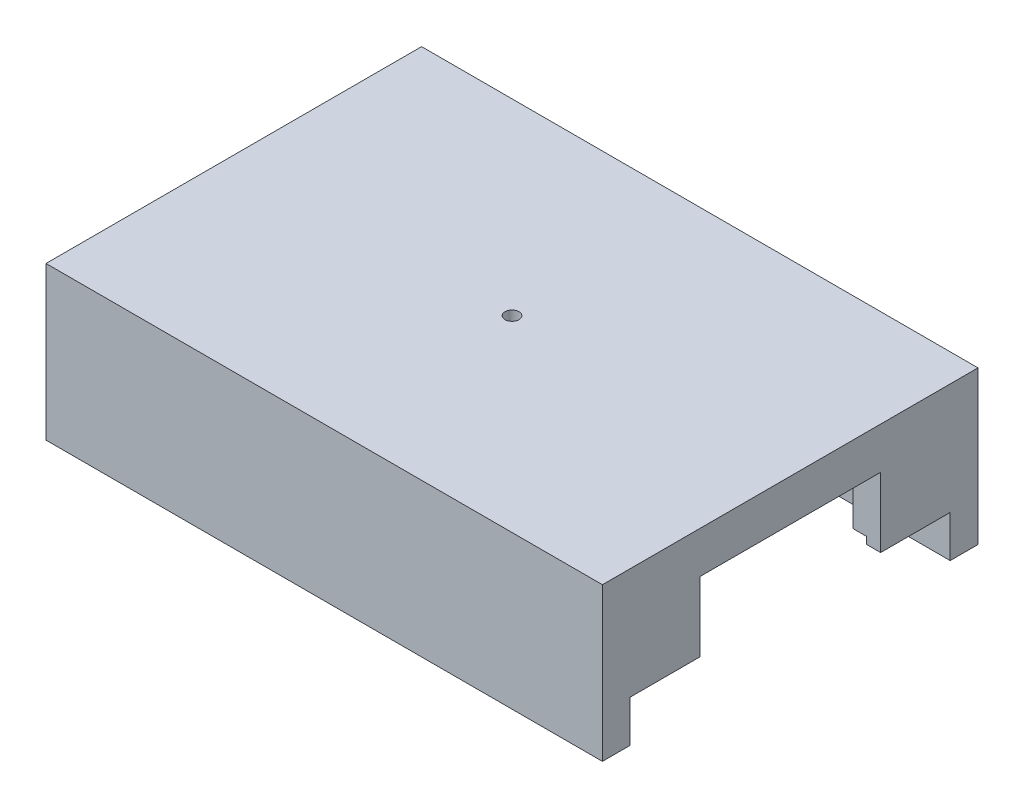
SolidWorks part; units mm, degrees
ref_plane "Front Plane" through (0, 0, 0) normal (0, 0, 1) x (1, 0, 0)
ref_plane "Top Plane" through (0, 0, 0) normal (0, 1, 0) x (1, 0, 0)
ref_plane "Right Plane" through (0, 0, 0) normal (1, 0, 0) x (0, 0, -1)
sketch "Sketch1" plane through (0, 0, 0) normal (0, 1, 0) x (1, 0, 0)
  line L1 (-11.5, 11.5) -> (11.5, 11.5)
  line L2 (-11.5, 11.5) -> (-11.5, -11.5)
  line L3 (-11.5, -11.5) -> (11.5, -11.5)
  line L4 (11.5, 11.5) -> (11.5, -11.5)
  line L5 (-11.5, 11.5) -> (11.5, -11.5) construction
  line L6 (-11.5, -11.5) -> (11.5, 11.5) construction
  point P0 (0, 0)
  dimension "D1" = 23
  dimension "D2" = 23
sketch "Sketch2" plane through (0, 0, 0) normal (0, 1, 0) x (1, 0, 0)
  line L0 (-10.5, 8.3787) -> (-10.5, -8.3787)
  line L1 (-5, -5) -> (5, -5)
  line L3 (-5, 5) -> (5, 5)
  line L5 (-5, -5) -> (5, 5) construction
  line L6 (-5, 5) -> (5, -5) construction
  line L7 (10.5, 8.3787) -> (10.5, -8.3787)
  line L8 (-10.5, 8.3787) -> (-8.8713, 6.75)
  line L9 (-8.8713, 6.75) -> (-9.5, 6.75)
  line L10 (-9.5, -6.75) -> (-8.8713, -6.75)
  line L11 (-10.5, 8.3787) -> (8.3787, -10.5)
  line L12 (-8.8713, -6.75) -> (-10.5, -8.3787)
  line L13 (-8.3787, 10.5) -> (10.5, -8.3787)
  line L15 (-10.5, -8.3787) -> (8.3787, 10.5)
  line L17 (-8.3787, -10.5) -> (10.5, 8.3787)
  line L19 (-9.5, -6.75) -> (9.5, -6.75)
  line L20 (-9.5, -6.75) -> (-9.5, 6.75)
  line L21 (-9.5, 6.75) -> (9.5, 6.75)
  line L22 (9.5, -6.75) -> (9.5, 6.75)
  line L23 (-9.5, -6.75) -> (9.5, 6.75) construction
  line L24 (-9.5, 6.75) -> (9.5, -6.75) construction
  arc A2 (-5, -5) -> (-5, 5) centre (-1.2418, 0) cw
  arc A3 (5, 5) -> (5, -5) centre (1.2582, 0) cw
  point P0 (0, 0)
  point P12 (0, 0)
  point P22 (0, 0)
  point P25 (0, 0)
  point P28 (0, 0)
  point P33 (-1.0607, -1.0607)
  point P38 (1.0607, 1.0607)
  point P43 (-1.0607, 1.0607)
  point P46 (1.0607, -1.0607)
  dimension "D1" = 19
sketch "Sketch3" plane through (0, 0, 0) normal (0, 1, 0) x (1, 0, 0)
  line L3 (20, -20) -> (-20, -20)
  line L4 (20, -20) -> (20, 20)
  line L5 (20, 20) -> (-20, 20)
  line L6 (-20, -20) -> (-20, 20)
  line L7 (20, -20) -> (-20, 20) construction
  line L8 (20, 20) -> (-20, -20) construction
  circle A0 centre (0, 0) radius 5
  circle A1 centre (0, 0) radius 0.5
  point P7 (0, 0)
  point P8 (-11.5, 0)
extrude "Boss-Extrude2" add sketch "Sketch3" against normal blind 3 contours L6 L3 L4 L5 A0 | A0 A1
sketch "Sketch4" plane through (0, -3, 0) normal (0, -1, 0) x (1, 0, 0)
  line L0 (0, 11.5) -> (0, -11.5)
  line L1 (20, -11.5) -> (-20, -11.5)
  line L2 (20, -11.5) -> (20, -13.5)
  line L3 (-20, -11.5) -> (-20, -13.5)
  line L4 (20, -13.5) -> (-20, -13.5)
  line L5 (20, 20) -> (20, -20) construction
  line L6 (-20, 20) -> (-20, -20) construction
  line L7 (8.8, 0) -> (-8.8, 0) construction
  line L8 (-20, 11.5) -> (-20, 13.5)
  line L9 (20, 13.5) -> (-20, 13.5)
  line L10 (20, 11.5) -> (20, 13.5)
  line L11 (20, 11.5) -> (-20, 11.5)
  point P4 (0, 0)
  line M6 (-20, 20) -> (-20, -20)
  line M8 (20, -20) -> (20, 20)
extrude "Boss-Extrude3" add sketch "Sketch4" along normal blind 8 contours L4 L1 M8 M6 | L11 L9 M8 M6
sketch "Sketch5" plane through (0, 0, -11.5) normal (0, 0, 1) x (1, 0, 0)
  line L0 (0, -3) -> (0, -8)
  line L1 (20, -3) -> (-20, -3) construction
  line L2 (0, -8) -> (0, -9.5)
  line L3 (20, -11) -> (-20, -11) construction
  line L4 (5, -8) -> (-5, -8)
  line L5 (5, -8) -> (5, -11)
  line L6 (5, -11) -> (-5, -11)
  line L7 (-5, -8) -> (-5, -11)
  line L8 (5, -8) -> (-5, -11) construction
  line L9 (5, -11) -> (-5, -8) construction
  line L13 (19, -7.5) -> (-19, -7.5)
  line L14 (19, -7.5) -> (19, -8.5)
  line L15 (19, -8.5) -> (-19, -8.5)
  line L16 (-19, -7.5) -> (-19, -8.5)
  line L17 (19, -7.5) -> (-19, -8.5) construction
  line L18 (19, -8.5) -> (-19, -7.5) construction
  dimension "D1" = 10
  dimension "D2" = 1
sketch "Sketch6" plane through (0, -3, 0) normal (0, -1, 0) x (1, 0, 0)
  line L1 (20, 11.5) -> (18, 11.5)
  line L2 (20, 11.5) -> (20, 6.5)
  line L3 (20, 6.5) -> (18, 6.5)
  line L4 (18, 11.5) -> (18, 6.5)
  line L5 (8.8, 0) -> (-8.8, 0) construction
  line L6 (20, -6.5) -> (18, -6.5)
  line L7 (18, -11.5) -> (18, -6.5)
  line L8 (20, -11.5) -> (18, -11.5)
  line L9 (20, -11.5) -> (20, -6.5)
  line L10 (0, -8.8) -> (0, 8.8) construction
  line L11 (-20, -11.5) -> (-20, -6.5)
  line L12 (-20, -11.5) -> (-18, -11.5)
  line L13 (-18, -11.5) -> (-18, -6.5)
  line L14 (-20, -6.5) -> (-18, -6.5)
  line L15 (-20, 6.5) -> (-18, 6.5)
  line L16 (-18, 11.5) -> (-18, 6.5)
  line L17 (-20, 11.5) -> (-18, 11.5)
  line L18 (-20, 11.5) -> (-20, 6.5)
extrude "Boss-Extrude5" add sketch "Sketch6" along normal blind 5
sketch "Sketch7" plane through (0, -3, 0) normal (0, -1, 0) x (-1, 0, 0)
  line L1 (-20, -13.5) -> (20, -13.5)
  line L2 (-20, -13.5) -> (-20, -20)
  line L3 (-20, -20) -> (20, -20)
  line L4 (20, -13.5) -> (20, -20)
extrude "Cut-Extrude1" cut sketch "Sketch7" against normal blind 3
sketch "Sketch8" plane through (0, -3, 0) normal (0, -1, 0) x (1, 0, 0)
  line L1 (20, -13.5) -> (-20, -13.5)
  line L2 (20, -13.5) -> (20, -20)
  line L3 (20, -20) -> (-20, -20)
  line L4 (-20, -13.5) -> (-20, -20)
extrude "Cut-Extrude2" cut sketch "Sketch8" against normal blind 3
extrude "Cut-Extrude3" cut sketch "Sketch5" against normal blind 1 and the other way up to next contours L15 L14 L13 L0 L4 L5 | L13 L16 L15 L7 L4 L0 | L15 L2 L4 L7 | L15 L5 L4 L2
mirror "Mirror2" about plane through (0, 0, 0) normal (0, 0, 1) of "Cut-Extrude3"
